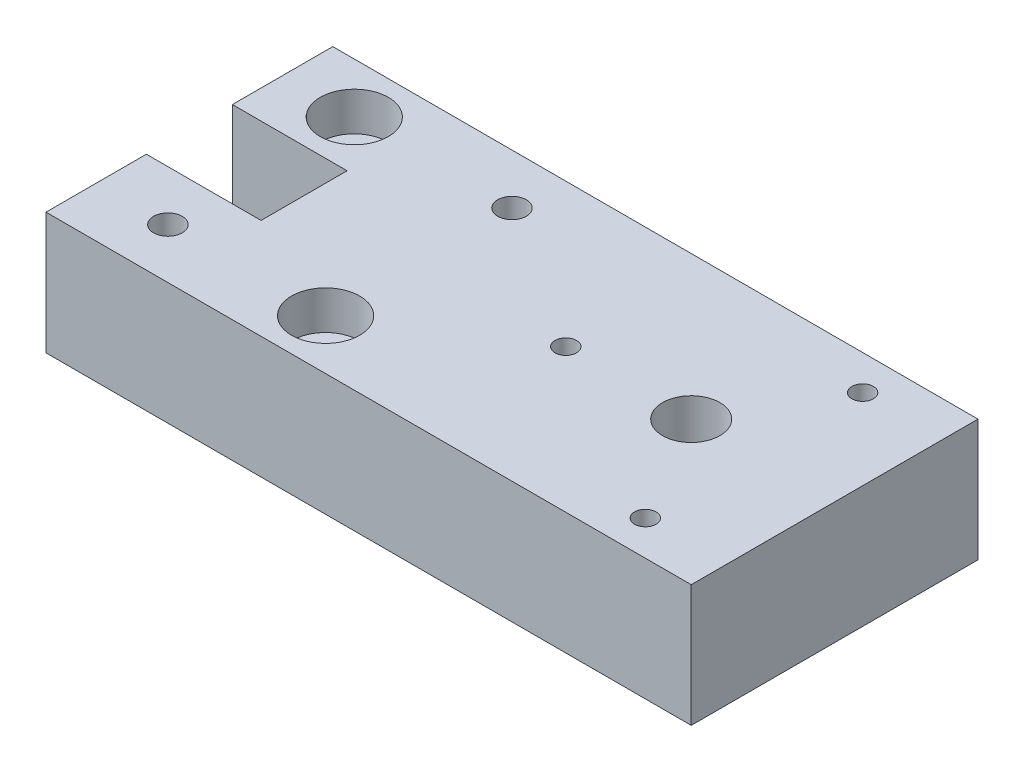
SolidWorks part; units mm, degrees
ref_plane "정면" through (0, 0, 0) normal (0, 0, 1) x (1, 0, 0)
ref_plane "윗면" through (0, 0, 0) normal (0, 1, 0) x (1, 0, 0)
ref_plane "우측면" through (0, 0, 0) normal (1, 0, 0) x (0, 0, -1)
sketch "스케치1" plane through (0, 0, 0) normal (0, 1, 0) x (1, 0, 0)
  line L0 (-90, -6) -> (-90, -20)
  line L1 (-90, 20) -> (0, 20)
  line L2 (-90, 20) -> (-90, 6)
  line L3 (-90, -20) -> (0, -20)
  line L4 (0, 20) -> (0, -20)
  line L5 (-90, 6) -> (-74, 6)
  line L7 (-90, -6) -> (-74, -6)
  line L8 (-74, 6) -> (-74, -6)
  dimension "D1" = 40
  dimension "D2" = 20
  dimension "D3" = 90
  dimension "D4" = 12
  dimension "D5" = 6
  dimension "D6" = 16
extrude "보스-돌출1" add sketch "스케치1" along normal blind 17
sketch "스케치4" plane through (0, 0, 0) normal (0, -1, 0) x (1, 0, 0)
  line L0 (-20, 0) -> (0, 34.641) construction
  line L1 (-20, 0) -> (0, -34.641) construction
  line L2 (0, 34.641) -> (0, -34.641) construction
  line L3 (-90, 6) -> (-90, 20) construction
  circle A1 centre (-80, -13) radius 2.75
  circle A2 centre (-80, 13) radius 2
  circle A3 centre (-58, 13) radius 2.75
  circle A4 centre (-58, -13) radius 2
  circle A5 centre (-20, 0) radius 17.5 construction
  circle A6 centre (-20, 0) radius 4
  circle A7 centre (-11.25, 15.1554) radius 1.5
  circle A8 centre (-11.25, -15.1554) radius 1.5
  circle A9 centre (-37.5, 0) radius 1.5
  point P19 (0, 0)
  point P20 (-80, -13)
  point P24 (-20, 0)
  dimension "D2" = 4
  dimension "D4" = 5.5
  dimension "D6" = 4
  dimension "D7" = 35
  dimension "D9" = 8
  dimension "D11" = 3
  dimension "D12" = 3
  dimension "D13" = 10
  dimension "D15" = 5.5
  dimension "D3" = 13
  dimension "D5" = 22
  dimension "D8" = 38
  dimension "D10" = 120
  dimension "D14" = 13
  dimension "D16" = 13
extrude "컷-돌출2" cut sketch "스케치4" against normal through all
sketch "스케치5" plane through (0, 17, 0) normal (0, 1, 0) x (1, 0, 0)
  circle A0 centre (-80, 13) radius 4.75
  circle A1 centre (-58, -13) radius 4.75
  dimension "D1" = 9.5
  dimension "D2" = 9.5
extrude "컷-돌출3" cut sketch "스케치5" against normal blind 5.4
hole_wizard "M4 여유 구멍1" positions "스케치9" profile "스케치11" hole size "M4" standard "KS"
sketch "스케치9" plane through (-74, 0, 0) normal (-1, 0, 0) x (0, 0, 1)
  line L0 (6, 17) -> (6, 0) construction
  line L2 (-6, 17) -> (6, 17) construction
  point P0 (0, 12)
  point P4 (0, 0)
  point P7 (0, 0)
  dimension "D1" = 6
  dimension "D2" = 5
sketch "스케치11" plane through (-74, 12, 0) normal (0, 1, 0) x (0, 0, 1)
  line L0 (0, 0) -> (0, 5.8026)
  line L1 (0, 5.8026) -> (3, 4)
  line L2 (3, 4) -> (3, 0)
  line L5 (3, 0) -> (0, 0)
  line L10 (0, 5.8026) -> (-3, 4) construction
  line L11 (0, -6.35) -> (0, 107.95) construction
  dimension "구멍 지름" = 6
  dimension "구멍 깊이" = 4
  dimension "드릴 각도" = 118
